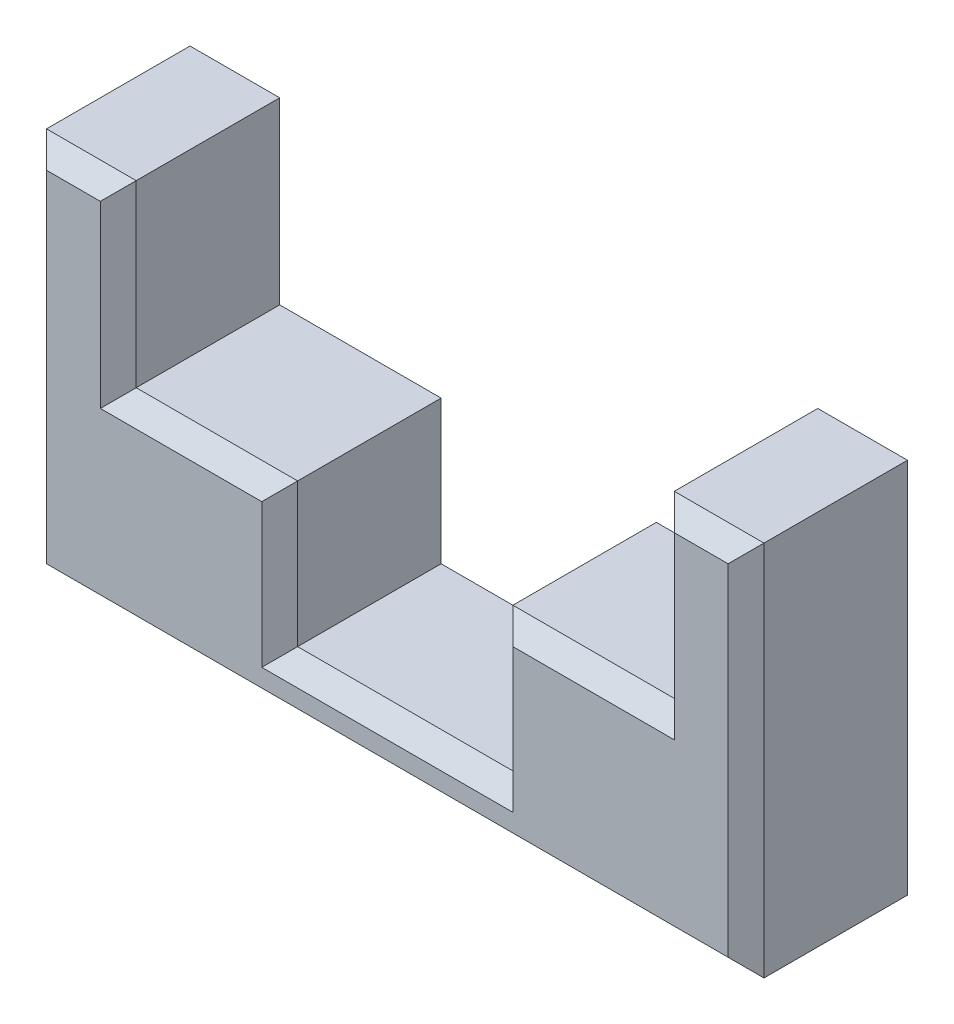
SolidWorks part; units mm, degrees
ref_plane "Front Plane" through (0, 0, 0) normal (0, 0, 1) x (1, 0, 0)
ref_plane "Top Plane" through (0, 0, 0) normal (0, 1, 0) x (1, 0, 0)
ref_plane "Right Plane" through (0, 0, 0) normal (1, 0, 0) x (0, 0, -1)
sketch "Sketch1" plane through (0, 0, 0) normal (0, 0, 1) x (1, 0, 0)
  line L0 (-14.2859, 0) -> (15.7141, 0) construction
  line L1 (-14.2859, 0) -> (-14.2859, -10)
  line L2 (15.7141, 0) -> (15.7141, -10)
  line L3 (0.7141, 0) -> (0.7141, -10) construction
  line L4 (-5.2859, -10) -> (6.7141, -10) construction
  line L5 (-5.2859, -10) -> (-5.2859, -18)
  line L6 (6.7141, -10) -> (6.7141, -18)
  line L7 (6.7141, -10) -> (15.7141, -10)
  line L8 (-5.2859, -10) -> (-14.2859, -10)
  line L9 (15.7141, 0) -> (20.7141, 0)
  line L10 (-19.2859, 0) -> (-14.2859, 0)
  line L11 (-5.2859, -18) -> (6.7141, -18)
  line L12 (0.7141, -18) -> (0.7141, -21) construction
  line L13 (-19.2859, 0) -> (-19.2859, -21)
  line L14 (-19.2859, -21) -> (20.7141, -21)
  line L15 (20.7141, -21) -> (20.7141, 0)
  point P3 (0.7141, 0)
  point P11 (0.7141, -10)
extrude "Boss-Extrude1" add sketch "Sketch1" along normal blind 10
chamfer "Chamfer1" distance 1 angle 45 24 edges at (20.7141, -10.5, 10) (0.7141, -21, 10) (-19.2859, -10.5, 10) (-16.7859, 0, 10) (-14.2859, -5, 10) (-9.7859, -10, 10) (-5.2859, -14, 10) (0.7141, -18, 10) (6.7141, -14, 10) (11.2141, -10, 10) (15.7141, -5, 10) (18.2141, 0, 10) (15.7141, -5, 0) (11.2141, -10, 0) (6.7141, -14, 0) (0.7141, -18, 0) (-5.2859, -14, 0) (-9.7859, -10, 0) (-14.2859, -5, 0) (-16.7859, 0, 0) (-19.2859, -10.5, 0) (0.7141, -21, 0) (20.7141, -10.5, 0) (18.2141, 0, 0)
